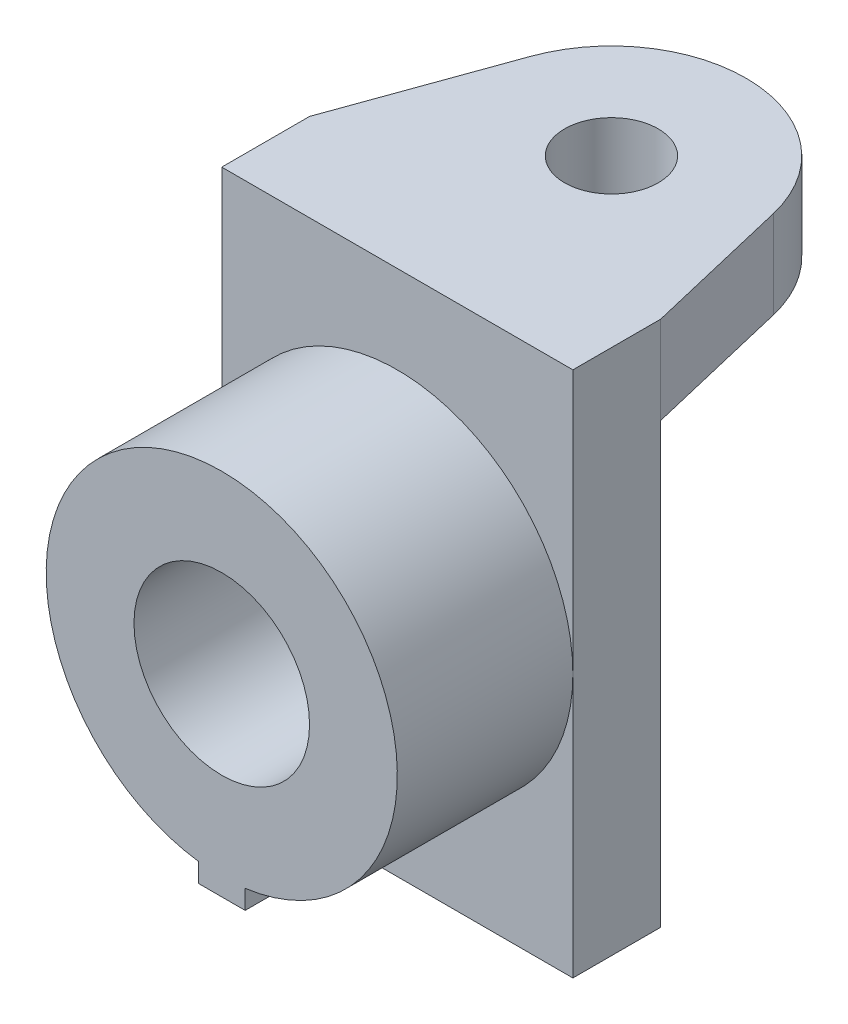
SolidWorks part; units mm, degrees
ref_plane "Front Plane" through (0, 0, 0) normal (0, 0, 1) x (1, 0, 0)
ref_plane "Top Plane" through (0, 0, 0) normal (0, 1, 0) x (1, 0, 0)
ref_plane "Right Plane" through (0, 0, 0) normal (1, 0, 0) x (0, 0, -1)
sketch "Sketch1" plane through (0, 0, 0) normal (0, 0, 1) x (1, 0, 0)
  line L1 (-37.1358, 25.5308) -> (22.8642, 25.5308)
  line L2 (-37.1358, 25.5308) -> (-37.1358, -64.4692)
  line L3 (-37.1358, -64.4692) -> (22.8642, -64.4692)
  line L4 (22.8642, 25.5308) -> (22.8642, -64.4692)
  dimension "D1" = 60
  dimension "D2" = 90
extrude "Boss-Extrude1" add sketch "Sketch1" along normal blind 15
sketch "Sketch2" plane through (0, 0, 15) normal (0, 0, 1) x (1, 0, 0)
  line L0 (-37.1358, -19.4692) -> (22.8642, -19.4692) construction
  line L1 (-37.1358, 25.5308) -> (-37.1358, -64.4692) construction
  line L2 (22.8642, -64.4692) -> (22.8642, 25.5308) construction
  line L3 (-11.1358, -49.2013) -> (-11.1358, -52.4692)
  line L6 (-11.1358, -52.4692) -> (-3.1358, -52.4692)
  line L7 (-3.1358, -49.2013) -> (-3.1358, -52.4692)
  arc A0 (-3.1358, -49.2013) -> (-11.1358, -49.2013) centre (-7.1358, -19.4692) ccw
  circle A1 centre (-7.1358, -19.4692) radius 15
  dimension "D1" = 60
  dimension "D2" = 30
extrude "Boss-Extrude2" add sketch "Sketch2" along normal blind 30 contours A0 L3 L6 L7 | A1
sketch "Sketch3" plane through (0, 25.5308, 0) normal (0, 1, 0) x (1, 0, 0)
  line L0 (-37.1358, -15) -> (22.8642, -15) construction
  line L1 (-7.1358, 0) -> (-37.1358, 0)
  line L2 (22.8642, 0) -> (-37.1358, 0) construction
  line L3 (-37.1358, 0) -> (-27.1515, 27.749)
  line L4 (-7.1358, 0) -> (22.8642, 0)
  line L5 (22.8642, 0) -> (16.8691, 25.2712)
  arc A0 (16.8691, 25.2712) -> (-27.1515, 27.749) centre (-5.5098, 19.9622) ccw
  circle A1 centre (-5.5098, 19.9622) radius 8
  point P6 (-7.1358, -15)
  dimension "D1" = 16
  dimension "D2" = 46
  dimension "D3" = 35
extrude "Boss-Extrude5" add sketch "Sketch3" against normal blind 15 contours A1 | A0 L3 L1 L4 L5
